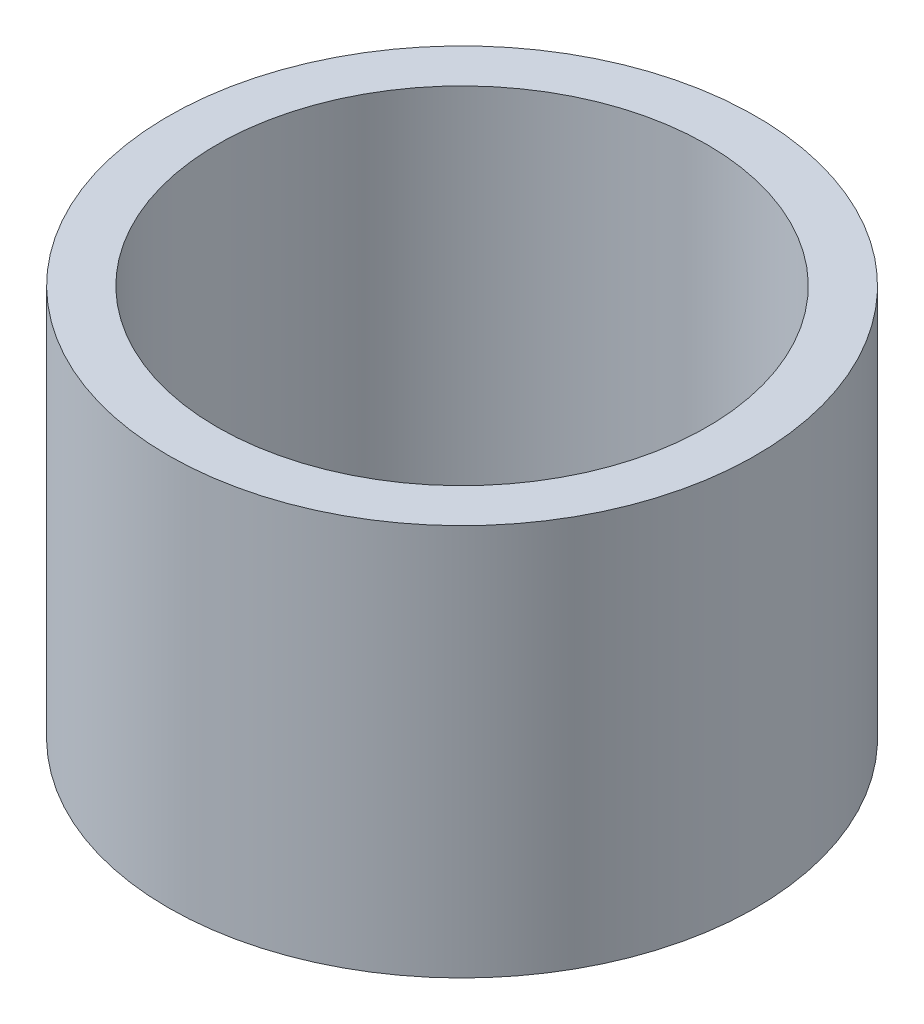
SolidWorks part; units mm, degrees
ref_plane "Front Plane" through (0, 0, 0) normal (0, 0, 1) x (1, 0, 0)
ref_plane "Top Plane" through (0, 0, 0) normal (0, 1, 0) x (1, 0, 0)
ref_plane "Right Plane" through (0, 0, 0) normal (1, 0, 0) x (0, 0, -1)
sketch "Sketch1" plane through (0, 0, 0) normal (0, 1, 0) x (1, 0, 0)
  circle A0 centre (0, 0) radius 0.25
  circle A1 centre (0, 0) radius 0.3
  dimension "D1" = 0.5
  dimension "D2" = 0.6
extrude "Boss-Extrude1" add sketch "Sketch1" along normal blind 0.4
sketch "Sketch2" plane through (0, 0, 0) normal (0, 0, 1) x (1, 0, 0)
  line L0 (-0.3, 0.2) -> (0.3, 0.2) construction
  line L1 (0.3, 0) -> (0.3, 0.4) construction
  line L2 (-0.3, 0.4) -> (-0.3, 0) construction
  point P4 (0, 0)
  point P7 (0, 0)
  point P9 (0.3, 0.2)
  dimension "D1" = 0.2
